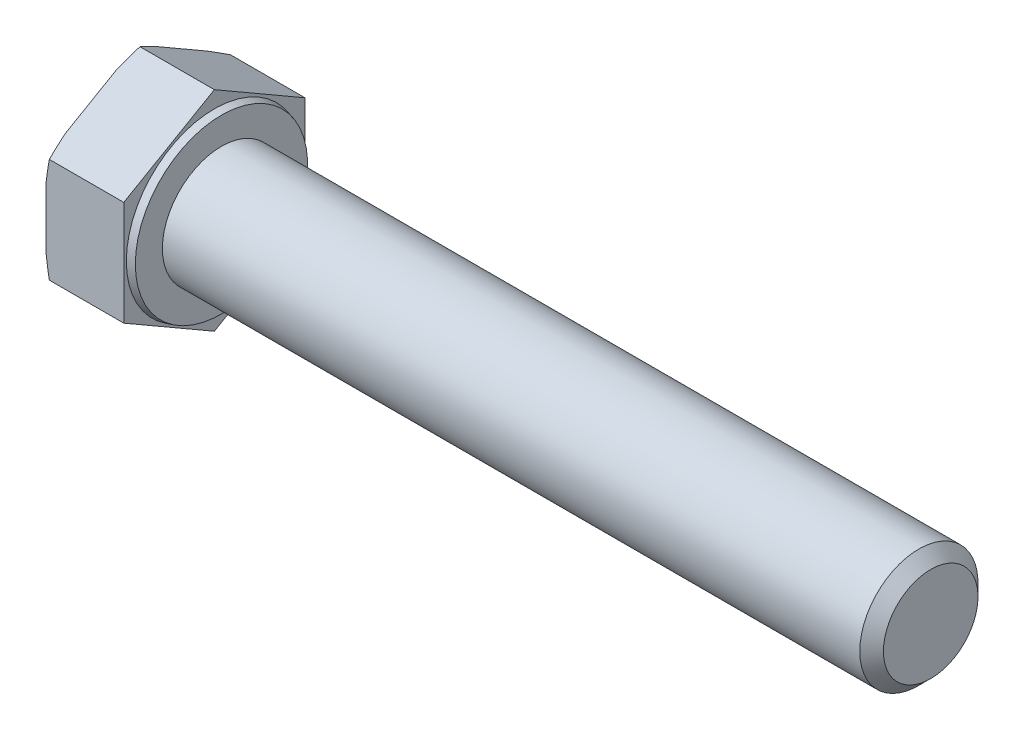
SolidWorks part; units mm, degrees
material "AISI 1020"
ref_plane "Спереди" through (0, 0, 0) normal (0, 0, 1) x (1, 0, 0)
ref_plane "Сверху" through (0, 0, 0) normal (0, 1, 0) x (1, 0, 0)
ref_plane "Справа" through (0, 0, 0) normal (1, 0, 0) x (0, 0, -1)
sketch "Эскиз1" plane through (0, 0, 0) normal (0, 0, 1) x (1, 0, 0)
  line L0 (-1000, 0) -> (49000, 0) construction
  line L1 (-6.58, 0) -> (-6.58, 8.85)
  line L2 (-6.58, 8.85) -> (0, 8.85)
  line L3 (0, 8.85) -> (0, 7.449)
  line L4 (0.6, 5) -> (60.6, 5)
  line L5 (60.6, 5) -> (60.6, 0)
  line L6 (-6.58, 0) -> (60.6, 0)
  line L7 (0, 7.449) -> (0.6, 7.2882)
  line L8 (0.6, 7.2882) -> (0.6, 5)
  line L9 (0.5, 0) -> (0.5, 7.315) construction
  dimension "_d" = 10
  dimension "D1" = 60
  dimension "D5" = 17.7
  dimension "D2" = 0.6
  dimension "D3" = 6.58
  dimension "D4" = 0.1
  dimension "D6" = 14.63
  dimension "D7" = 75
revolve "Повернуть1" add sketch "Эскиз1" angle 360 about L0
sketch "Эскиз2" plane through (-6.58, 0, 0) normal (-1, 0, 0) x (0, 0, 1)
  line L1 (0, -8.85) -> (7.6643, -4.425)
  line L2 (7.6643, -4.425) -> (7.6643, 4.425)
  line L3 (7.6643, 4.425) -> (0, 8.85)
  line L4 (0, 8.85) -> (-7.6643, 4.425)
  line L5 (-7.6643, 4.425) -> (-7.6643, -4.425)
  line L6 (-7.6643, -4.425) -> (0, -8.85)
  circle A0 centre (0, 0) radius 7.6643 construction
  circle A1 centre (0, 0) radius 8.85 construction
extrude "Вырез-Вытянуть1" cut sketch "Эскиз2" against normal through all flip side to cut
sketch "Эскиз4" plane through (0, 0, 0) normal (0, 0, 1) x (1, 0, 0)
  line L0 (-1000, 0) -> (49000, 0) construction
  line L1 (-6.58, 8.075) -> (-6.2979, 8.85)
  line L2 (-6.2979, 8.85) -> (-6.58, 8.85)
  line L3 (-6.58, 8.85) -> (-6.58, 8.075)
  line L4 (-6.58, 4.425) -> (-6.58, 8.85) construction
  line L6 (0, 8.85) -> (-6.58, 8.85) construction
  dimension "D1" = 20
  dimension "D2" = 16.15
revolve "Вырез-Повернуть1" cut sketch "Эскиз4" angle 360 about L0
chamfer "Фаска1" distance 1 angle 45 1 edges at (60.6, 0, 5)
equation "\"l\" = 60'длина болта"
equation "\"_d\"= 10'диаметр болта"
equation "\"b\"= 20'длина резьбы"
equation "\"k\"= 6.58'толщина шляпки"
equation "\"e\"= 17.7'диаметр головки описанный"
equation "\"S\"= 17'размер под ключ"
equation "\"_d@Эскиз1\"=\"_d\""
equation "\"dw\"= 14.63"
equation "\"da\"= 9.78"
equation "\"с\"= 0.6"
equation "\"D1@Эскиз1\"=\"l\""
equation "\"D5@Эскиз1\"=\"e\""
equation "\"D2@Эскиз1\"=\"с\""
equation "\"D3@Эскиз1\"=\"k\""
equation "\"D2@Эскиз4\"=\"S\"*0.95"
equation "\"D1@Фаска1\"=\"_d\"/10"
equation "\"D6@Эскиз1\"=\"dw\""
